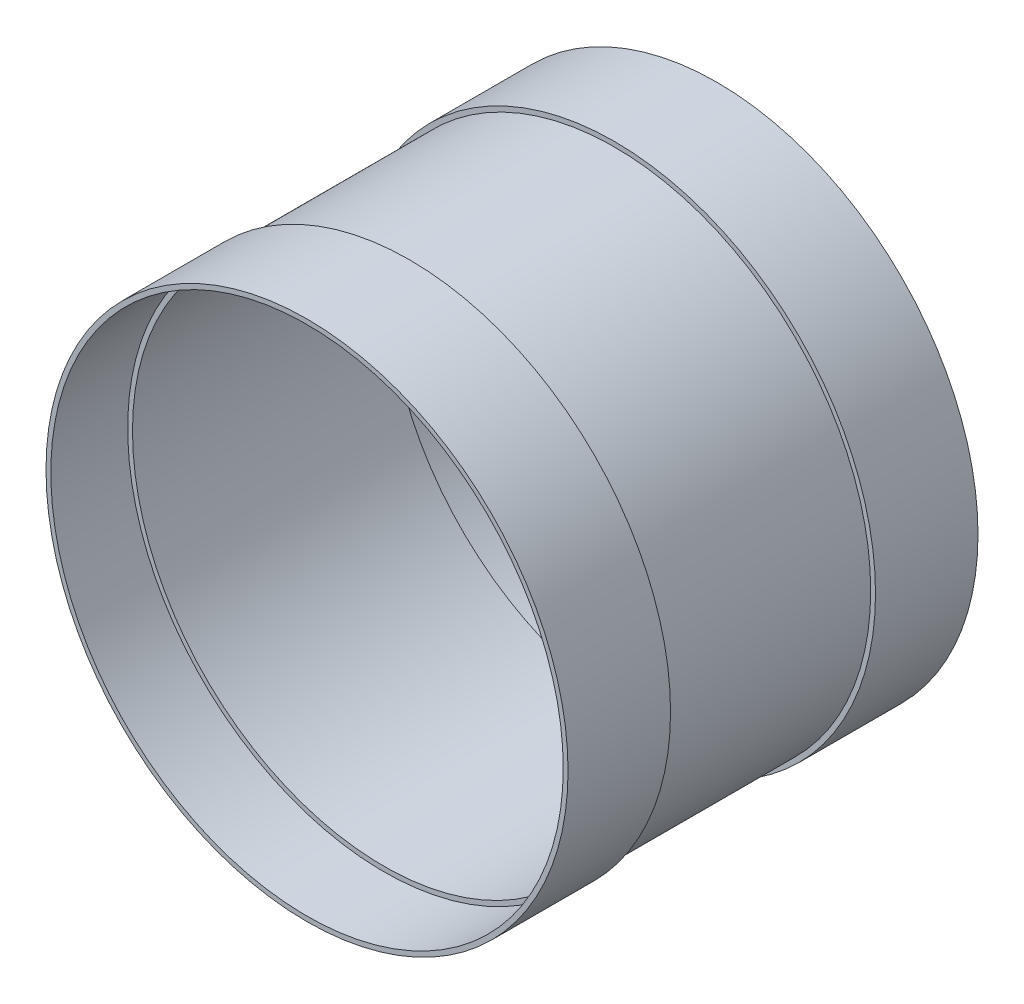
SolidWorks part; units mm, degrees
ref_plane "Front" through (0, 0, 0) normal (0, 0, 1) x (1, 0, 0)
ref_plane "Top" through (0, 0, 0) normal (0, 1, 0) x (1, 0, 0)
ref_plane "Right" through (0, 0, 0) normal (1, 0, 0) x (0, 0, -1)
sketch "Sketch2" plane through (0, 0, 0) normal (1, 0, 0) x (0, 0, -1)
  line L0 (-62.5946, 0) -> (53.5645, 0) construction
  line L1 (-203.2, 258.7625) -> (-101.6, 258.7625)
  line L2 (-101.6, 258.7625) -> (-101.6, 254)
  line L7 (-101.6, 254) -> (-203.2, 254)
  line L8 (-203.2, 254) -> (-203.2, 258.7625)
  line L9 (0, 0) -> (0, 72.5353) construction
  line L11 (101.6, 258.7625) -> (203.2, 258.7625)
  line L12 (101.6, 258.7625) -> (101.6, 254)
  line L13 (101.6, 254) -> (203.2, 254)
  line L14 (203.2, 258.7625) -> (203.2, 254)
  point P13 (203.2, 256.3813)
  dimension "D1" = 101.6
  dimension "D2" = 4.7625
  dimension "D3" = 406.4
  dimension "D4" = 508
revolve "Revolve1" add sketch "Sketch2" angle 360 about L0
sketch "Sketch3" plane through (0, 0, 0) normal (1, 0, 0) x (0, 0, -1)
  line L1 (-127, 249.2375) -> (127, 249.2375)
  line L2 (-127, 249.2375) -> (-127, 254)
  line L3 (-127, 254) -> (127, 254)
  line L4 (127, 249.2375) -> (127, 254)
  line L6 (0, 0) -> (103.0496, 0) construction
  line L7 (-101.6, 254) -> (-203.2, 254) construction
  line L8 (-203.2, 258.7625) -> (-203.2, -258.7625) construction
  line L9 (203.2, -258.7625) -> (203.2, 258.7625) construction
  dimension "D1" = 4.7625
  dimension "D2" = 76.2
  dimension "D3" = 76.2
revolve "Revolve2" add sketch "Sketch3" angle 360 about L6
